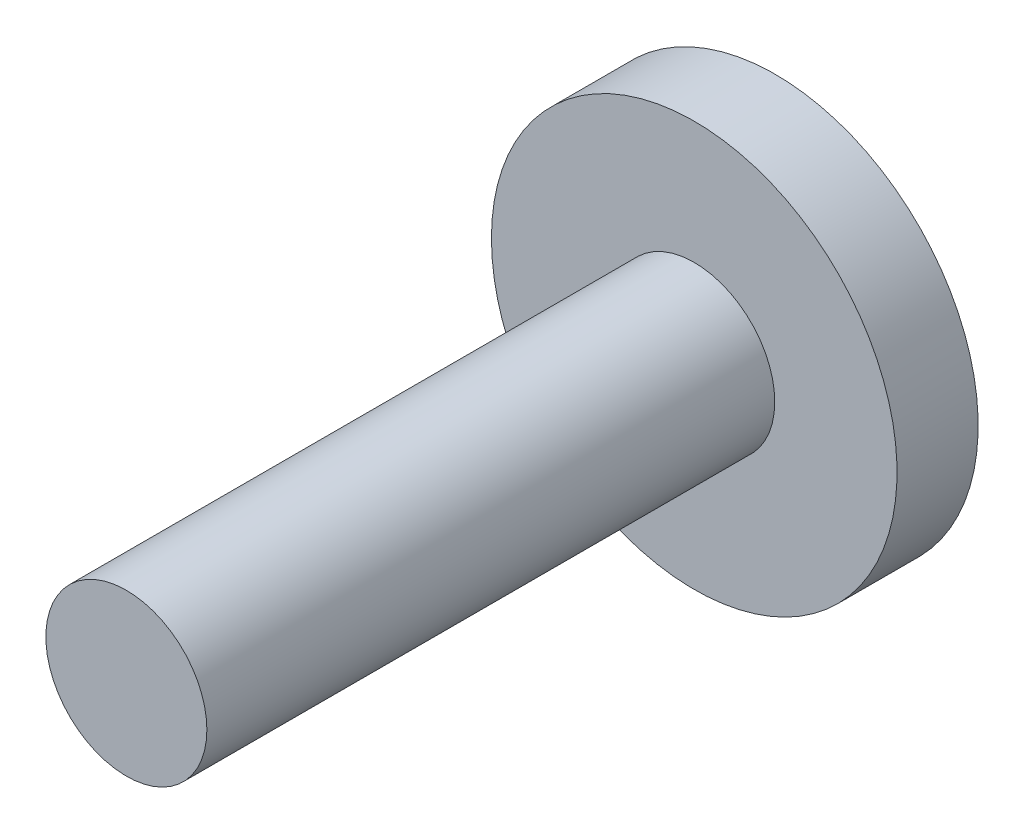
SolidWorks part; units mm, degrees
ref_plane "Alzado" through (0, 0, 0) normal (0, 0, 1) x (1, 0, 0)
ref_plane "Planta" through (0, 0, 0) normal (0, 1, 0) x (1, 0, 0)
ref_plane "Vista lateral" through (0, 0, 0) normal (1, 0, 0) x (0, 0, -1)
sketch "Croquis1" plane through (0, 0, 0) normal (0, 0, 1) x (1, 0, 0)
  circle A0 centre (0, 0) radius 1.985
  dimension "D1" = 3.97
extrude "Saliente-Extruir1" add sketch "Croquis1" along normal blind 14
sketch "Croquis2" plane through (0, 0, 0) normal (0, 0, -1) x (-1, 0, 0)
  circle A0 centre (0, 0) radius 5
  dimension "D1" = 10
extrude "Saliente-Extruir2" add sketch "Croquis2" along normal blind 2
